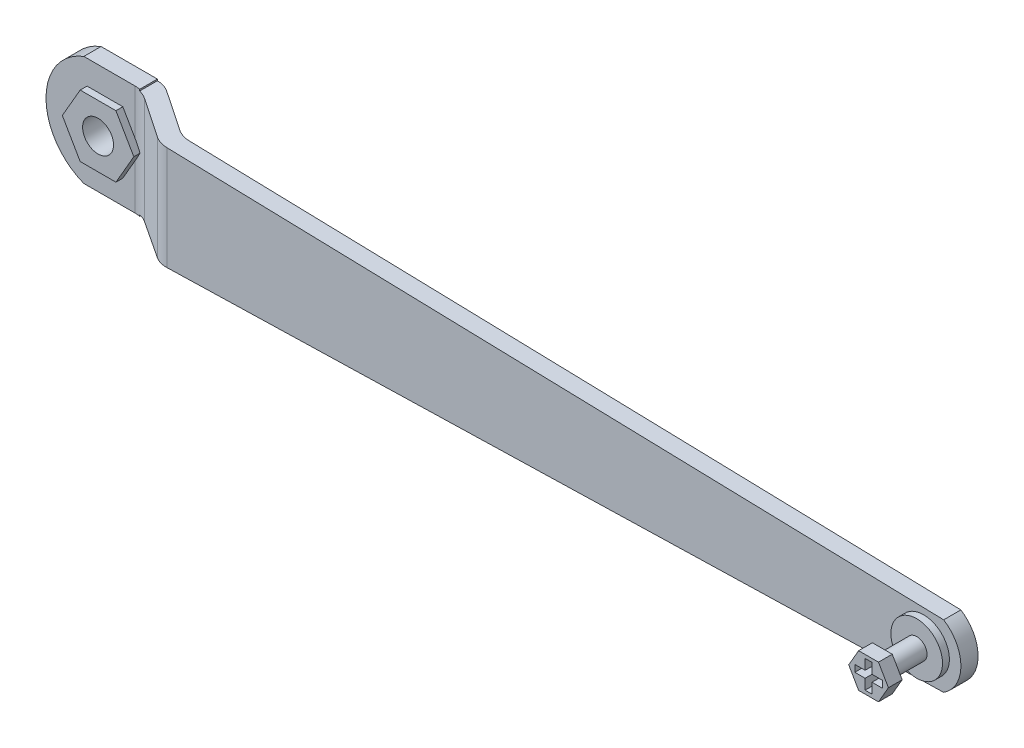
SolidWorks part; units mm, degrees
ref_plane "Front Plane" through (0, 0, 0) normal (0, 0, 1) x (1, 0, 0)
ref_plane "Top Plane" through (0, 0, 0) normal (0, 1, 0) x (1, 0, 0)
ref_plane "Right Plane" through (0, 0, 0) normal (1, 0, 0) x (0, 0, -1)
sketch "Sketch1" plane through (0, 0, 0) normal (0, 1, 0) x (1, 0, 0)
  line L0 (0, 0) -> (28, 0)
  line L1 (28, 0) -> (43, -10)
  line L2 (43, -10) -> (276, -10)
  line L3 (0, 5) -> (29.5139, 5)
  line L4 (29.5139, 5) -> (44.5139, -5)
  line L5 (44.5139, -5) -> (276, -5)
  line L6 (0, 5) -> (0, 0)
  line L7 (276, -5) -> (276, -10)
  dimension "D1" = 28
  dimension "D2" = 15
  dimension "D3" = 233
  dimension "D4" = 10
  dimension "D5" = 5
extrude "Boss-Extrude1" add sketch "Sketch1" along normal blind 32
fillet "Fillet1" radius 7 4 edges at (44.5139, 16, 5) (29.5139, 16, -5) (43, 16, 10) (28, 16, 0)
sketch "Sketch4" plane through (0, 0, -5) normal (0, 0, -1) x (-1, 0, 0)
  line L0 (-27.3944, 32) -> (0, 32) construction
  line L1 (-27.3944, 0) -> (0, 0) construction
  line L2 (0, 32) -> (0, 0) construction
  line L3 (-11, 32) -> (12.6834, 39.3484)
  line L4 (12.6834, 39.3484) -> (11.5605, -17.3566)
  line L5 (11.5605, -17.3566) -> (-11, 0)
  arc A0 (-11, 32) -> (-11, 0) centre (-17.1364, 16) cw
  dimension "D1" = 11
  dimension "D2" = 11
extrude "Cut-Extrude1" cut sketch "Sketch4" against normal blind 32
sketch "Sketch5" plane through (0, 0, -5) normal (0, 0, -1) x (-1, 0, 0)
  line L0 (-11, 32) -> (-276, 25)
  line L1 (0, 16) -> (-92.4931, 16) construction
  line L2 (-276, 32) -> (-276, 0) construction
  line L3 (-276, 32) -> (-276, 0)
  line L4 (-276, 32) -> (-11, 32)
  line L5 (-276, 0) -> (-11, 0)
  line L6 (-11, 0) -> (-276, 7)
  arc A0 (-11, 0) -> (-11, 32) centre (-17.1364, 16) ccw construction
  line M7 (-27.3944, 32) -> (-27.3944, 0)
  dimension "D1" = 18
extrude "Cut-Extrude2" cut sketch "Sketch5" against normal blind 32 contours L4 L3 L0 M7 | L6 L3 L5 M7
sketch "Sketch6" plane through (0, 0, 5) normal (0, 0, -1) x (-1, 0, 0)
  line L0 (-45.1194, 31.0987) -> (-276, 25) construction
  line L1 (-45.1194, 0.9013) -> (-276, 7) construction
  line L2 (-276, 25) -> (-276, 7) construction
  line L3 (-271, 25.1321) -> (-282.9169, 26.4016)
  line L4 (-282.9169, 26.4016) -> (-282.2096, 2.158)
  line L5 (-282.2096, 2.158) -> (-271, 6.8679)
  line L6 (-271, 6.8679) -> (-270.947, 6.7828)
  arc A0 (-271, 25.1321) -> (-271, 6.8679) centre (-265.1605, 16) ccw
  line M1 (-276, 25) -> (-276, 7)
  line M2 (-276, 7) -> (-46.6333, 0.9413)
  line M4 (-46.6333, 31.0587) -> (-276, 25)
  dimension "D1" = 5
extrude "Cut-Extrude3" cut sketch "Sketch6" against normal blind 32 contours A0 M4 M1 | A0 M1 M2
sketch "Sketch7" plane through (0, 0, 10) normal (0, 0, 1) x (1, 0, 0)
  circle A0 centre (265.1605, 16) radius 3
  dimension "D1" = 6
extrude "Boss-Extrude2" add sketch "Sketch7" along normal blind 12
sketch "Sketch8" plane through (0, 0, 22) normal (0, 0, 1) x (1, 0, 0)
  line L1 (270.934, 16) -> (268.0473, 21)
  line L2 (268.0473, 21) -> (262.2738, 21)
  line L3 (262.2738, 21) -> (259.387, 16)
  line L4 (259.387, 16) -> (262.2738, 11)
  line L5 (262.2738, 11) -> (268.0473, 11)
  line L6 (268.0473, 11) -> (270.934, 16)
  circle A0 centre (265.1605, 16) radius 5 construction
  dimension "D1" = 10
extrude "Boss-Extrude3" add sketch "Sketch8" along normal blind 4
sketch "Sketch9" plane through (0, 0, 26) normal (0, 0, 1) x (1, 0, 0)
  line L1 (264.1605, 20) -> (266.1605, 20)
  line L2 (264.1605, 20) -> (264.1605, 12)
  line L3 (264.1605, 12) -> (266.1605, 12)
  line L4 (266.1605, 20) -> (266.1605, 12)
  line L5 (264.1605, 20) -> (266.1605, 12) construction
  line L6 (264.1605, 12) -> (266.1605, 20) construction
  line L7 (261.1605, 17) -> (269.1605, 17)
  line L8 (261.1605, 17) -> (261.1605, 15)
  line L9 (261.1605, 15) -> (269.1605, 15)
  line L10 (269.1605, 17) -> (269.1605, 15)
  line L11 (261.1605, 17) -> (269.1605, 15) construction
  line L12 (261.1605, 15) -> (269.1605, 17) construction
  point P0 (265.1605, 16)
  point P6 (265.1605, 16)
  dimension "D1" = 2
  dimension "D2" = 2
  dimension "D3" = 8
  dimension "D4" = 8
extrude "Cut-Extrude4" cut sketch "Sketch9" against normal blind 4 contours L10 L7 L4 L9 | L2 L7 L4 L1 | L2 L9 L4 L7 | L8 L9 L2 L7 | L9 L2 L3 L4
sketch "Sketch10" plane through (0, 0, 10) normal (0, 0, 1) x (1, 0, 0)
  circle A0 centre (265.1605, 16) radius 7.5
  dimension "D1" = 15
extrude "Boss-Extrude4" add sketch "Sketch10" along normal blind 2
sketch "Sketch11" plane through (0, 0, 0) normal (0, 0, 1) x (1, 0, 0)
  line L1 (27.5287, 16) -> (22.3325, 25)
  line L2 (22.3325, 25) -> (11.9402, 25)
  line L3 (11.9402, 25) -> (6.7441, 16)
  line L4 (6.7441, 16) -> (11.9402, 7)
  line L5 (11.9402, 7) -> (22.3325, 7)
  line L6 (22.3325, 7) -> (27.5287, 16)
  circle A0 centre (17.1364, 16) radius 9 construction
extrude "Boss-Extrude5" add sketch "Sketch11" along normal blind 2
sketch "Sketch12" plane through (0, 0, 2) normal (0, 0, 1) x (1, 0, 0)
  line L6 (22.3325, 7) -> (27.5287, 16)
  line L7 (27.5287, 16) -> (22.3325, 25)
  line L8 (22.3325, 25) -> (11.9402, 25)
  line L9 (11.9402, 25) -> (6.7441, 16)
  line L10 (6.7441, 16) -> (11.9402, 7)
  line L11 (11.9402, 7) -> (22.3325, 7)
  line L12 (22.3325, 7) -> (27.5287, 16)
  line L13 (27.5287, 16) -> (22.3325, 25)
  line L14 (22.3325, 25) -> (11.9402, 25)
  line L15 (11.9402, 25) -> (6.7441, 16)
  line L16 (6.7441, 16) -> (11.9402, 7)
  line L17 (11.9402, 7) -> (22.3325, 7)
  dimension "D1" = 0
extrude "Boss-Extrude6" add sketch "Sketch12" against normal blind 9
sketch "Sketch17" plane through (0, 0, 2) normal (0, 0, 1) x (1, 0, 0)
  line L0 (17.1364, 7) -> (17.1364, 25) construction
  line L1 (11.9402, 7) -> (22.3325, 7) construction
  line L2 (22.3325, 25) -> (11.9402, 25) construction
  circle A0 centre (17.1364, 16) radius 4.5
  dimension "D1" = 9
extrude "Cut-Extrude5" cut sketch "Sketch17" against normal blind 10
